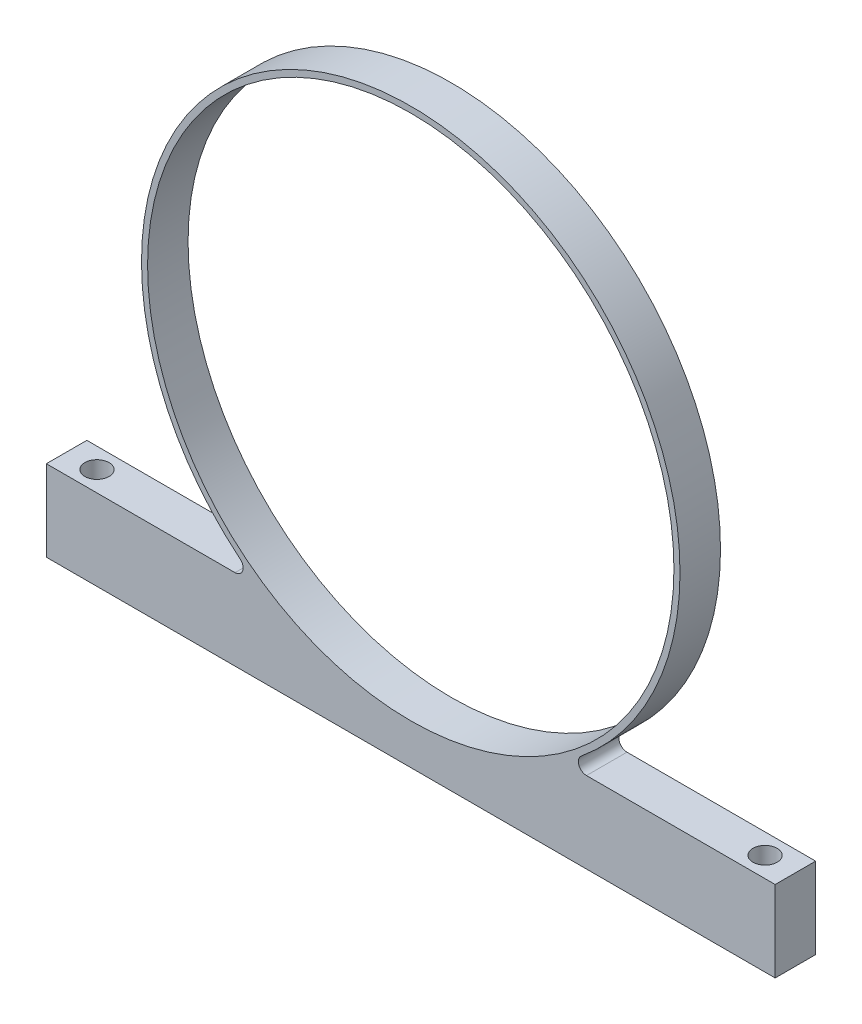
SolidWorks part; units mm, degrees
material "6061-T6 (SS)"
ref_plane "Front Plane" through (0, 0, 0) normal (0, 0, 1) x (1, 0, 0)
ref_plane "Top Plane" through (0, 0, 0) normal (0, 1, 0) x (1, 0, 0)
ref_plane "Right Plane" through (0, 0, 0) normal (1, 0, 0) x (0, 0, -1)
sketch "Sketch1" plane through (0, 0, 0) normal (0, 0, 1) x (1, 0, 0)
  line L0 (0, 0) -> (0, -41.275) construction
  line L1 (-23.7362, -34.925) -> (-57.15, -34.925)
  line L2 (57.15, -34.925) -> (23.7362, -34.925)
  line L3 (57.15, -34.925) -> (57.15, -47.625)
  line L4 (57.15, -47.625) -> (-57.15, -47.625)
  line L5 (-57.15, -34.925) -> (-57.15, -47.625)
  line L6 (57.15, -34.925) -> (-57.15, -47.625) construction
  line L7 (57.15, -47.625) -> (-57.15, -34.925) construction
  circle A0 centre (0, 0) radius 41.275
  arc A1 (23.7362, -34.925) -> (-23.7362, -34.925) centre (0, 0) ccw
  dimension "D1" = 82.55
  dimension "D5" = 84.455
  dimension "D2" = 41.275
  dimension "D3" = 114.3
  dimension "D4" = 12.7
extrude "Boss-Extrude1" add sketch "Sketch1" along normal blind 6.35
fillet "Fillet1" radius 1.27 2 edges at (-23.7362, -34.925, 3.175) (23.7362, -34.925, 3.175)
hole_wizard "#6 Clearance Hole1" positions "Sketch3" profile "Sketch2" hole size "#6" standard "Ansi Inch"
sketch "Sketch3" plane through (0, -47.625, 0) normal (0, -1, 0) x (1, 0, 0)
  line L0 (57.15, 3.175) -> (-57.15, 3.175) construction
  line L1 (57.15, 6.35) -> (57.15, 0) construction
  line L2 (-57.15, 6.35) -> (-57.15, 0) construction
  point P0 (-52.3875, 3.175)
  point P1 (52.3875, 3.175)
  dimension "D1" = 4.7625
  dimension "D2" = 4.7625
sketch "Sketch2" plane through (-52.3875, -47.625, 3.175) normal (1, 0, 0) x (0, 0, -1)
  line L0 (0, 0) -> (0, 26.5408)
  line L1 (0, 26.5408) -> (1.8986, 25.4)
  line L2 (1.8986, 25.4) -> (1.8986, 0)
  line L5 (1.8986, 0) -> (0, 0)
  line L10 (0, 26.5408) -> (-1.8986, 25.4) construction
  line L11 (0, -6.35) -> (0, 107.95) construction
  dimension "Hole Dia." = 3.7973
  dimension "Hole Depth" = 25.4
  dimension "Drill Angle" = 118
